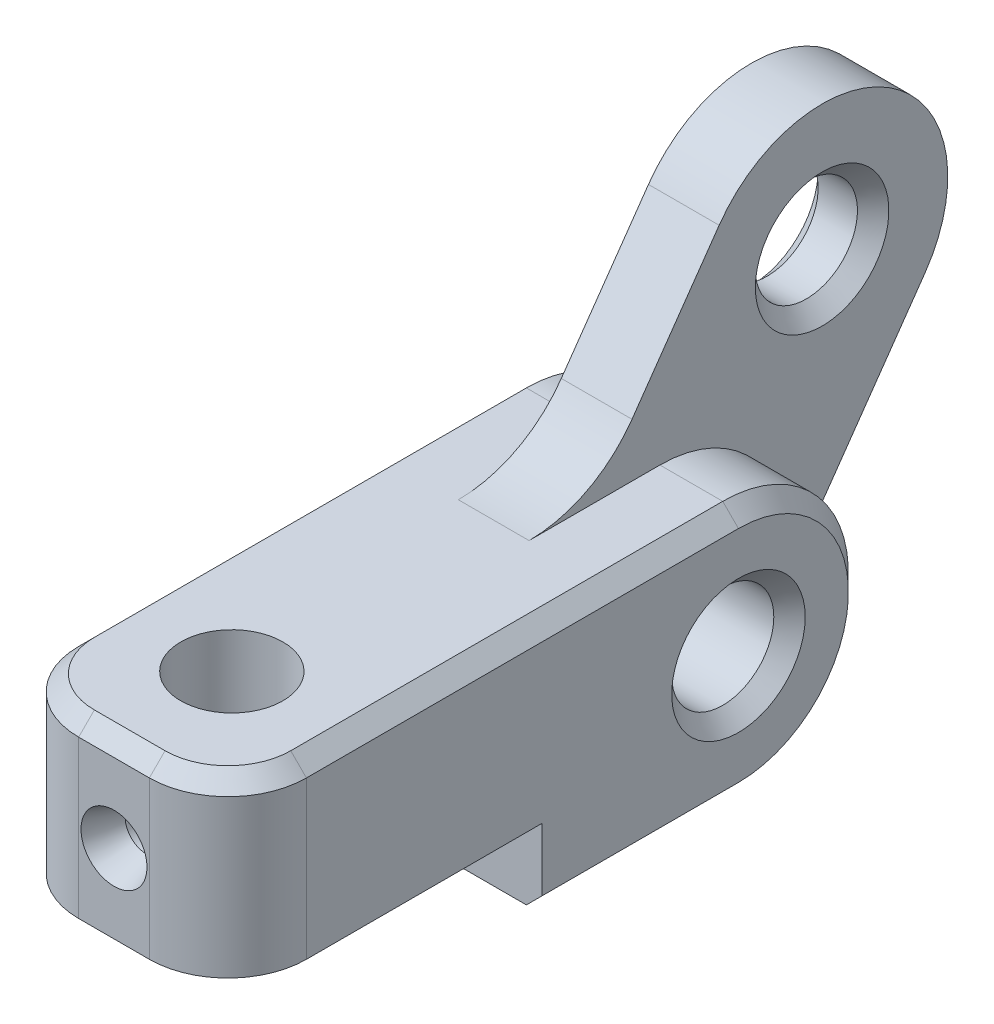
SolidWorks part; units mm, degrees
ref_plane "Top Plane" through (0, 0, 0) normal (0, 0, 1) x (1, 0, 0)
ref_plane "Right Plane" through (0, 0, 0) normal (0, 1, 0) x (1, 0, 0)
ref_plane "Front Plane" through (0, 0, 0) normal (1, 0, 0) x (0, 0, -1)
sketch "Sketch1" plane through (0, 0, 0) normal (1, 0, 0) x (0, 0, -1)
  line L0 (0, 0) -> (-25, 0) construction
  line L1 (0, 0) -> (10.3244, 14.7447) construction
  line L2 (-1.7759, 11.4114) -> (3.7712, 19.3333)
  line L3 (-8.3291, 8) -> (-25, 8)
  line L4 (6.5532, -4.5886) -> (16.8776, 10.1561)
  line L5 (0, -8) -> (-25, -8) construction
  line L6 (-4.1645, 8) -> (3.7712, 19.3333) construction
  line L7 (-4.1645, 8) -> (-25, 8) construction
  line L8 (4.1645, -8) -> (16.8776, 10.1561) construction
  line L9 (4.1645, -8) -> (-25, -8) construction
  line L10 (-25, 0) -> (-32.5, 0) construction
  line L11 (-25, 8) -> (-32.5, 8)
  line L12 (-25, -8) -> (-32.5, -8) construction
  line L13 (-25, 8) -> (-25, -8) construction
  line L14 (-32.5, 8) -> (-32.5, -8) construction
  line L15 (-32.5, -3) -> (-12.5, -3)
  line L16 (-12.5, -3) -> (-12.5, -8)
  line L17 (-32.5, 8) -> (-32.5, -3)
  line L18 (-12.5, -8) -> (0, -8)
  circle A0 centre (0, 0) radius 3.25
  circle A3 centre (10.3244, 14.7447) radius 3.25
  arc A4 (3.7712, 19.3333) -> (16.8776, 10.1561) centre (10.3244, 14.7447) cw
  arc A6 (-1.7759, 11.4114) -> (-8.3291, 8) centre (-8.3291, 16) cw
  arc A7 (6.5532, -4.5886) -> (0, -8) centre (0, 0) cw
  dimension "D1" = 6.5
  dimension "D3" = 8
  dimension "D7" = 8
  dimension "D2" = 125
  dimension "D4" = 18
  dimension "D5" = 25
  dimension "D8" = 7.5
  dimension "D9" = 20
  dimension "D10" = 5
  dimension "D6" = 8
extrude "Boss-Extrude1" add sketch "Sketch1" along normal mid plane 4.5
sketch "Sketch2" plane through (2.25, 0, 0) normal (1, 0, 0) x (0, 0, -1)
  line L0 (-32.5, 8) -> (0, 8)
  line L2 (-32.5, 8) -> (-32.5, -3)
  line L3 (-32.5, -3) -> (-12.5, -3)
  line L4 (-12.5, -3) -> (-12.5, -8)
  line L5 (-12.5, -8) -> (0, -8)
  arc A0 (0, -8) -> (0, 8) centre (0, 0) ccw
  circle A1 centre (0, 0) radius 3.25 construction
  circle A2 centre (0, 0) radius 3.25
extrude "Boss-Extrude2" add sketch "Sketch2" along normal blind 5
mirror "Mirror1" about plane through (0, 0, 0) normal (1, 0, 0) of "Boss-Extrude2"
sketch "Sketch3" plane through (0, -3, 0) normal (0, -1, 0) x (1, 0, 0)
  line L0 (0, 32.5) -> (0, 25) construction
  line L1 (7.25, 32.5) -> (-7.25, 32.5) construction
  circle A0 centre (0, 25) radius 3.25
  dimension "D2" = 6.5
  dimension "D1" = 7.5
extrude "Cut-Extrude1" cut sketch "Sketch3" against normal through all
fillet "Fillet1" radius 5 2 edges at (7.25, 2.5, 32.5) (-7.25, 2.5, 32.5)
chamfer "Chamfer1" distance 1 angle 45 13 edges at (0, 8, 32.5) (5.7855, 8, 31.0355) (-5.7855, 8, 31.0355) (-2.25, 14.7447, -13.5744) (2.25, 14.7447, -13.5744) (7.25, -8, 6.25) (7.25, 0, -8) (7.25, 8, 13.75) (7.25, 0, -3.25) (-7.25, 8, 13.75) (-7.25, 0, -8) (-7.25, -8, 6.25) (-7.25, 0, -3.25)
sketch "Sketch4" plane through (0, 0, 32.5) normal (0, 0, 1) x (1, 0, 0)
  line L0 (0, 7) -> (0, -3) construction
  line L1 (2.25, 7) -> (-2.25, 7) construction
  line L2 (7.25, -3) -> (-7.25, -3) construction
  circle A0 centre (0, 2) radius 1.35
  dimension "D1" = 2.7
extrude "Cut-Extrude2" cut sketch "Sketch4" against normal up to next
chamfer "Chamfer2" distance 0.75 angle 70 1 edges at (1.35, 2, 32.5)
chamfer "Chamfer3" distance 1 angle 45 1 edges at (0, -3, 21.75)
